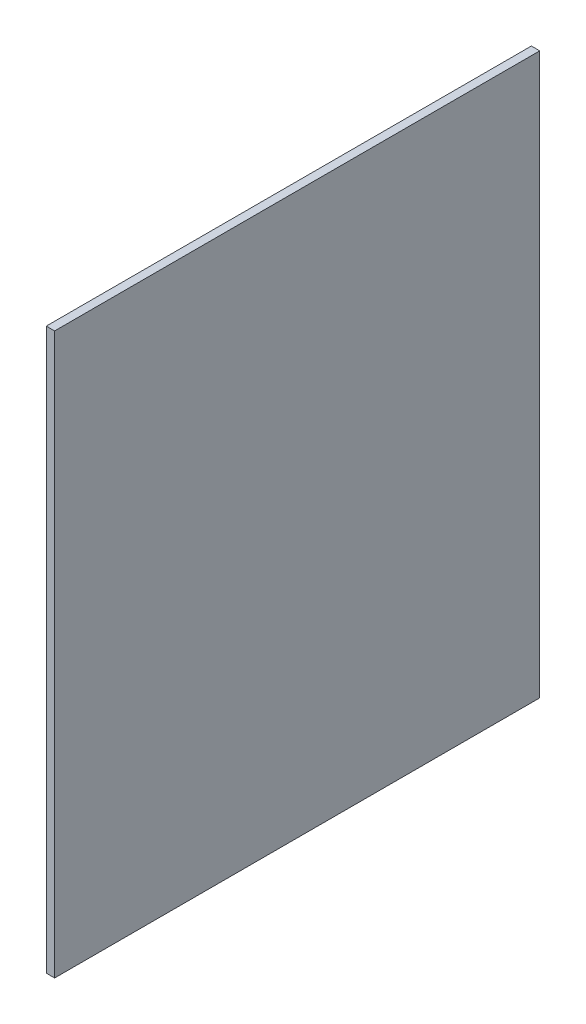
SolidWorks part; units mm, degrees
ref_plane "Plan de face" through (0, 0, 0) normal (0, 0, 1) x (1, 0, 0)
ref_plane "Plan de dessus" through (0, 0, 0) normal (0, 1, 0) x (1, 0, 0)
ref_plane "Plan de droite" through (0, 0, 0) normal (1, 0, 0) x (0, 0, -1)
sketch "Esquisse1" plane through (0, 0, 0) normal (1, 0, 0) x (0, 0, -1)
  line L1 (-101.0751, 38.956) -> (478.9249, 38.956)
  line L2 (-101.0751, 38.956) -> (-101.0751, -631.044)
  line L3 (-101.0751, -631.044) -> (478.9249, -631.044)
  line L4 (478.9249, 38.956) -> (478.9249, -631.044)
  dimension "D1" = 580
  dimension "D2" = 670
extrude "Boss.-Extru.1" add sketch "Esquisse1" along normal blind 10
equation "\"ProfondeurPlacard\"=580"
equation "\"D1@Esquisse1\"=\"ProfondeurPlacard\""
equation "\"EpaisseurPlaque\"= 10"
equation "\"LargeurPlacard\"=160+70+135"
equation "\"DistanceAvantSyphon\"=240"
equation "\"DistanceAvantEvier\"=100"
equation "\"DiametreTuyau\"=90"
equation "\"HauteurTuyau\"=430"
equation "\"LargeurAeration\"=260"
equation "\"HauteurAeration\"=340"
equation "\"AerationSol\"=210"
equation "\"AerationAvant\"=270"
equation "\"ProfondeurCharniere\"=80"
equation "\"HauteurCharniere\"=60"
equation "\"LargeurCharniere\"=60"
equation "\"HauteurPlacard\"=650"
equation "\"HauteurEvier\"=\"HauteurPlacard\"-555"
equation "\"HauteurDroitEvier\"=\"HauteurPlacard\" -500"
equation "\"HauteurSolSyphon\"=320"
equation "\"DiametreSyphon\"=70"
equation "\"PositionSyphonCoteGauche\"=160"
equation "\"D2@Esquisse1\"=\"HauteurPlacard\"+2 * \"EpaisseurPlaque\""
